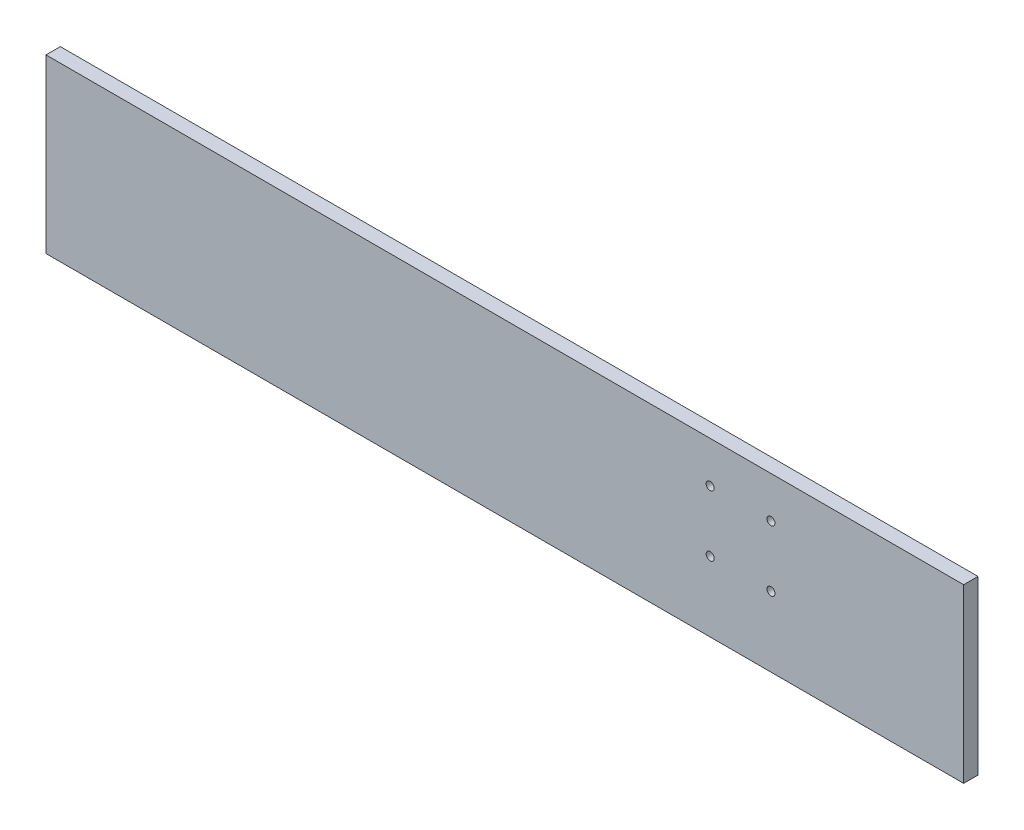
SolidWorks part; units mm, degrees
ref_plane "Front Plane" through (0, 0, 0) normal (0, 0, 1) x (1, 0, 0)
ref_plane "Top Plane" through (0, 0, 0) normal (0, 1, 0) x (1, 0, 0)
ref_plane "Right Plane" through (0, 0, 0) normal (1, 0, 0) x (0, 0, -1)
sketch "Sketch1" plane through (0, 0, 0) normal (0, 0, 1) x (1, 0, 0)
  line L1 (0, 0) -> (406.4, 0)
  line L2 (0, 0) -> (0, 76.2)
  line L3 (0, 76.2) -> (406.4, 76.2)
  line L4 (406.4, 0) -> (406.4, 76.2)
  dimension "D1" = 76.2
  dimension "D2" = 406.4
extrude "Boss-Extrude1" add sketch "Sketch1" along normal blind 6.35
sketch "Sketch2" plane through (0, 0, 6.35) normal (0, 0, 1) x (1, 0, 0)
  circle A0 centre (294.1124, 57.9371) radius 1.778
  circle A1 centre (321.0531, 57.9596) radius 1.778
  circle A2 centre (321.0756, 31.0188) radius 1.778
  circle A3 centre (294.1349, 30.9963) radius 1.778
extrude "Cut-Extrude1" cut sketch "Sketch2" against normal blind 10.16
